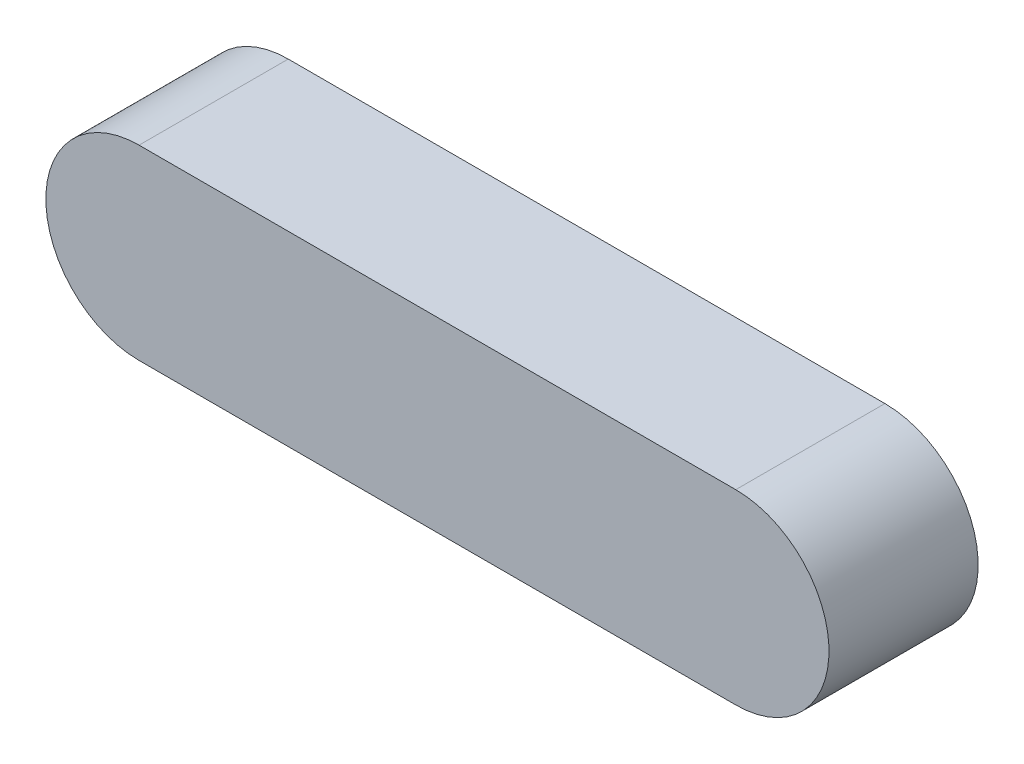
SolidWorks part; units mm, degrees
ref_plane "Front Plane" through (0, 0, 0) normal (0, 0, 1) x (1, 0, 0)
ref_plane "Top Plane" through (0, 0, 0) normal (0, 1, 0) x (1, 0, 0)
ref_plane "Right Plane" through (0, 0, 0) normal (1, 0, 0) x (0, 0, -1)
sketch "Sketch2" plane through (0, 0, 0) normal (0, 0, 1) x (1, 0, 0)
  line L0 (-11.4953, 0) -> (20.5047, 0) construction
  line L1 (-11.4953, 5) -> (20.5047, 5)
  line L2 (-11.4953, -5) -> (20.5047, -5)
  arc A0 (-11.4953, 5) -> (-11.4953, -5) centre (-11.4953, 0) ccw
  arc A1 (20.5047, -5) -> (20.5047, 5) centre (20.5047, 0) ccw
  point P3 (4.5047, 0)
  dimension "D1" = 5
  dimension "D2" = 32
extrude "Boss-Extrude1" add sketch "Sketch2" along normal blind 8
